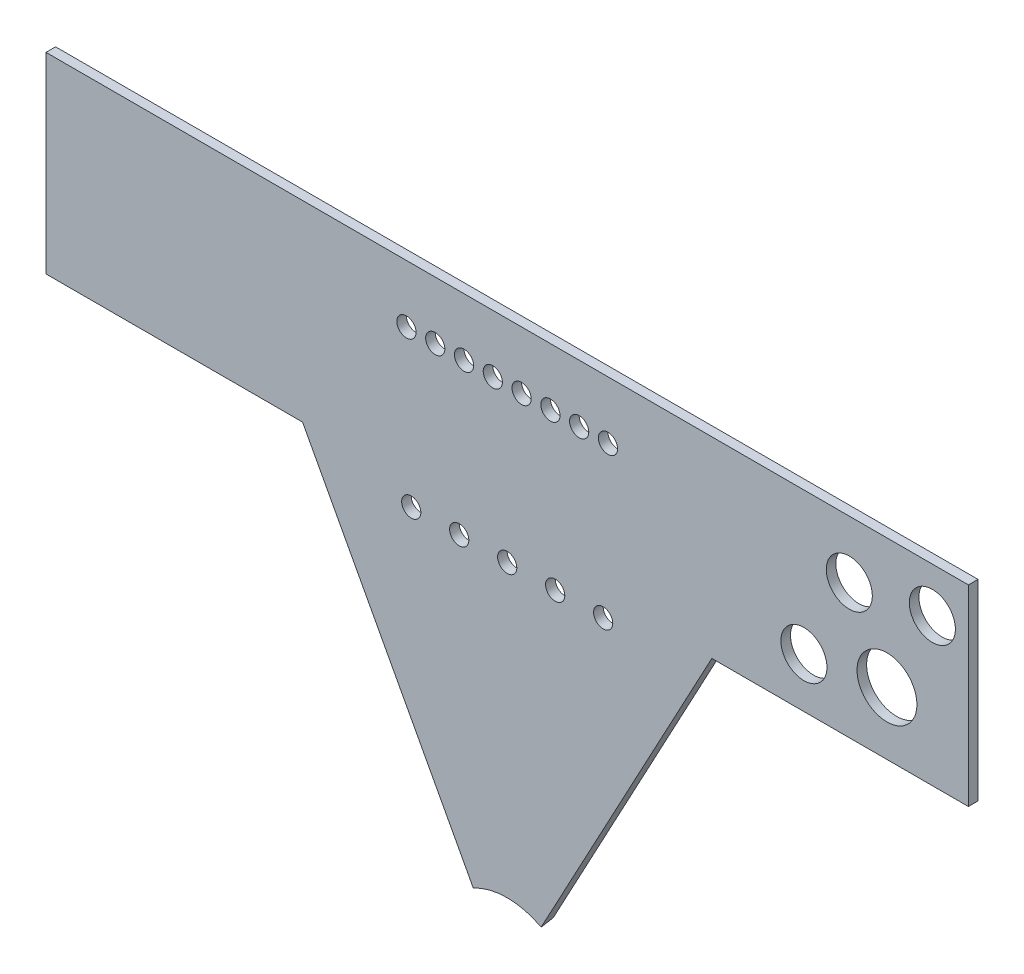
SolidWorks part; units mm, degrees
other "Markup1"
sketch "Sketch14" plane through (-149.406, -168.7453, 3.175) normal (0, 0, 1) x (1, 0, 0)
other "DetailItem1"
other "DetailItem2"
other "DetailItem3"
other "DetailItem4"
other "DetailItem5"
other "DetailItem6"
other "Markup2"
sketch "Sketch15" plane through (-149.406, -168.7453, 3.175) normal (0, 0, 1) x (1, 0, 0)
ref_plane "Front Plane" through (0, 0, 0) normal (0, 0, 1) x (1, 0, 0)
ref_plane "Top Plane" through (0, 0, 0) normal (0, 1, 0) x (1, 0, 0)
ref_plane "Right Plane" through (0, 0, 0) normal (1, 0, 0) x (0, 0, -1)
sketch "Sketch1" plane through (0, 0, 0) normal (0, 0, 1) x (1, 0, 0)
  line L0 (-101.781, 0) -> (101.781, 0)
  line L1 (-101.781, 0) -> (-12.0294, -167.2577)
  line L2 (101.781, 0) -> (12.0294, -167.2577)
  line L3 (0, -164.2341) -> (0, 0) construction
  arc A0 (-12.0294, -167.2577) -> (12.0294, -167.2577) centre (0, -189.6754) cw
  point P4 (0, 0)
  dimension "D1" = 203.5619
  dimension "D2" = 61.782
  dimension "D3" = 189.817
  dimension "D4" = 61.782
  dimension "D5" = 189.817
extrude "Boss-Extrude1" add sketch "Sketch1" along normal blind 3.175 draft 28
sketch "Sketch6" plane through (0, 0, 3.175) normal (0, 0, 1) x (1, 0, 0)
  line L0 (-101.781, 0) -> (101.781, 0)
  line L1 (101.781, 0) -> (103.6968, 0)
  line L2 (12.6904, -169.5964) -> (104.6027, 1.6882) construction
  line L3 (103.6968, 0) -> (104.6027, 1.6882)
  line L4 (104.6027, 1.6882) -> (-104.6027, 1.6882)
  line L5 (104.6027, 1.6882) -> (-104.6027, 1.6882) construction
  line L6 (-104.6027, 1.6882) -> (-103.6968, 0)
  line L7 (-103.6968, 0) -> (-101.781, 0)
  line L8 (-104.6027, 1.6882) -> (-12.6904, -169.5964) construction
  line L9 (-101.781, 0) -> (-11.2312, -168.7453)
  line L10 (-101.781, 0) -> (-12.0294, -167.2577) construction
  line L11 (-12.6904, -169.5964) -> (-103.6968, 0)
  line L12 (101.781, 0) -> (11.2312, -168.7453)
  line L14 (12.6904, -169.5964) -> (103.6968, 0)
  arc A0 (12.6904, -169.5964) -> (-12.6904, -169.5964) centre (0, -189.6754) ccw construction
  arc A2 (-11.2312, -168.7453) -> (-12.6904, -169.5964) centre (0, -189.6754) ccw
  arc A3 (11.2312, -168.7453) -> (12.6904, -169.5964) centre (0, -189.6754) cw
  line M7 (12.6904, -169.5964) -> (104.6027, 1.6882)
  line M9 (-104.6027, 1.6882) -> (-12.6904, -169.5964)
extrude "Cut-Extrude3" cut sketch "Sketch6" against normal through all contours A2 L9 L7 M9 | L12 A3 L1 M7
sketch "Sketch8" plane through (0, 0, 3.175) normal (0, 0, 1) x (1, 0, 0)
  line L0 (-101.781, 0) -> (-152.581, 0)
  line L1 (-152.581, 0) -> (-152.581, -63.5)
  line L2 (-152.581, -63.5) -> (-67.7065, -63.5)
  line L3 (-101.781, 0) -> (-12.0294, -167.2577) construction
  line L4 (-67.7065, -63.5) -> (-101.781, 0)
  line L5 (0, -1.7463) -> (0, 1.7463) construction
  line L6 (152.581, -63.5) -> (67.7065, -63.5)
  line L7 (101.781, 0) -> (152.581, 0)
  line L8 (152.581, 0) -> (152.581, -63.5)
  line L9 (67.7065, -63.5) -> (101.781, 0)
  dimension "D1" = 50.8
  dimension "D2" = 63.5
sketch "Sketch7" plane through (0, 0, 3.175) normal (0, 0, 1) x (1, 0, 0)
  line L0 (-98.3735, -6.35) -> (98.3735, -6.35) construction
  line L1 (-101.781, 0) -> (-12.0294, -167.2577) construction
  line L2 (101.781, 0) -> (12.0294, -167.2577) construction
  line L3 (-101.781, 0) -> (101.781, 0) construction
  line L4 (-83.9606, -6.35) -> (0.7672, -164.2457) construction
  circle A0 centre (-44.4493, -6.35) radius 1.016
  circle A1 centre (-31.7495, -6.35) radius 1.016
  circle A2 centre (-19.0497, -6.35) radius 1.016
  circle A3 centre (-6.3499, -6.35) radius 1.016
  circle A4 centre (6.3499, -6.35) radius 1.016
  circle A5 centre (19.0497, -6.35) radius 1.016
  circle A6 centre (31.7495, -6.35) radius 1.016
  circle A7 centre (44.4493, -6.35) radius 1.016
  arc A8 (12.0294, -167.2577) -> (-12.0294, -167.2577) centre (0, -189.6754) ccw construction
  circle A9 centre (-71.9506, -28.7313) radius 1.016
  dimension "D2" = 2.032
  dimension "D7" = 2.032
  dimension "D1" = 6.35
  dimension "D3" = 53.9242
  dimension "D5" = 53.9242
  dimension "D6" = 12.7
  dimension "D8" = 25.4
  dimension "D4" = 8
extrude "Boss-Extrude2" add sketch "Sketch8" against normal up to surface (3.175 mm away) up to face at (0, -82.873, 0)
sketch "Sketch9" plane through (0, 0, 3.175) normal (0, 0, 1) x (1, 0, 0)
  line L0 (0, 0) -> (0, -165.9223) construction
  line L1 (0, -165.9223) -> (33.8523, -158.9562) construction
  line L2 (-152.581, -19.05) -> (152.581, -19.05) construction
  line L3 (-152.581, 0) -> (-152.581, -63.5) construction
  line L4 (152.581, -63.5) -> (152.581, 0) construction
  line L5 (-152.581, 0) -> (152.581, 0) construction
  line L6 (153.5303, 9.145) -> (97.7491, -94.8067) construction
  line L7 (101.781, 0) -> (12.0294, -167.2577) construction
  line L8 (120.5165, -5.3742) -> (72.2981, -95.2324) construction
  arc A0 (11.2312, -168.7453) -> (-11.2312, -168.7453) centre (0, -189.6754) ccw construction
  circle A1 centre (125.6397, -42.8308) radius 9.906
  circle A2 centre (140.6521, -14.8542) radius 7.62
  circle A3 centre (113.178, -19.05) radius 7.62
  circle A4 centre (98.1656, -47.0266) radius 7.62
  point P19 (140.6521, -14.8542)
  point P20 (136.6993, -15.5058)
  point P21 (-33.3375, -19.05)
  point P22 (-23.8125, -19.05)
  point P23 (-14.2875, -19.05)
  point P24 (-4.7625, -19.05)
  point P31 (98.1656, -47.0266)
  point P32 (113.178, -19.05)
  point P37 (137.8545, -13.353)
  point P38 (113.1885, -19.05)
  point P39 (0, 0)
  dimension "D8" = 15.24
  dimension "D10" = 15.24
  dimension "D11" = 15.24
  dimension "D1" = 19.05
  dimension "D2" = 41.275
  dimension "D4" = 9.525
  dimension "D5" = 9.525
  dimension "D6" = 9.525
  dimension "D7" = 33.3375
  dimension "D9" = 22.225
  dimension "D12" = 31.75
  dimension "D3" = 31.75
hole_wizard "1/4 (0.25) Diameter Hole1" positions "Sketch10" profile "Sketch12" hole size "1/4" standard "ANSI Inch" end condition through all
sketch "Sketch10" plane through (0, 0, 3.175) normal (0, 0, 1) x (1, 0, 0)
  point P0 (-33.3375, -19.05)
  point P3 (-23.8125, -19.05)
  point P6 (-14.2875, -19.05)
  point P9 (-4.7625, -19.05)
sketch "Sketch12" plane through (-33.3375, -19.05, 3.175) normal (1, 0, 0) x (0, -1, 0)
  line L0 (0, 0) -> (0, 3.175)
  line L1 (0, 3.175) -> (3.175, 3.175)
  line L2 (3.175, 3.175) -> (3.175, 0)
  line L5 (3.175, 0) -> (0, 0)
  line L11 (0, -6.35) -> (0, 107.95) construction
  dimension "Thru Hole Dia." = 6.35
  dimension "Thru Hole Depth" = 3.175
ref_plane "Plane1" through (0, 0, 0) normal (1, 0, 0) x (0, 0, -1)
mirror "Mirror1" about plane through (0, 0, 0) normal (1, 0, 0) of "1/4 (0.25) Diameter Hole1"
extrude "Cut-Extrude4" cut sketch "Sketch9" against normal through all
sketch "Sketch16" plane through (0, 0, 3.175) normal (0, 0, 1) x (1, 0, 0)
  line L0 (-99.008, -69.85) -> (119.1387, -69.85) construction
  line L1 (0, -48.9613) -> (0, -108.1795) construction
  line L2 (-152.581, -63.5) -> (-67.7065, -63.5) construction
  point P7 (-15.875, -69.85)
  point P8 (-31.75, -69.85)
  point P9 (0, -69.85)
  point P10 (15.875, -69.85)
  point P11 (31.75, -69.85)
  dimension "D1" = 6.35
  dimension "D2" = 15.875
  dimension "D3" = 15.875
  dimension "D4" = 15.875
  dimension "D5" = 15.875
hole_wizard "1/4 (0.25) Diameter Hole2" positions "Sketch17" profile "Sketch18" hole size "1/4" standard "ANSI Inch" end condition through all
sketch "Sketch17" plane through (0, 0, 3.175) normal (0, 0, 1) x (1, 0, 0)
  point P0 (-31.75, -69.85)
  point P3 (-15.875, -69.85)
  point P6 (0, -69.85)
  point P9 (15.875, -69.85)
  point P12 (31.75, -69.85)
sketch "Sketch18" plane through (-31.75, -69.85, 3.175) normal (1, 0, 0) x (0, -1, 0)
  line L0 (0, 0) -> (0, 3.175)
  line L1 (0, 3.175) -> (3.175, 3.175)
  line L2 (3.175, 3.175) -> (3.175, 0)
  line L5 (3.175, 0) -> (0, 0)
  line L11 (0, -6.35) -> (0, 107.95) construction
  dimension "Thru Hole Dia." = 6.35
  dimension "Thru Hole Depth" = 3.175
equation "\"D4@Sketch1\"=\"D2@Sketch1\""
equation "\"D5@Sketch1\"=\"D3@Sketch1\""
equation "\"D5@Sketch7\"=\"D3@Sketch7\""
equation "\"D7@Sketch9\"=3.5*\"D4@Sketch9\""
equation "\"D5@Sketch9\"=\"D4@Sketch9\""
equation "\"D6@Sketch9\"=\"D4@Sketch9\""
equation "\"D3@Sketch16\"=\"D2@Sketch16\""
equation "\"D4@Sketch16\"=\"D2@Sketch16\""
equation "\"D5@Sketch16\"=\"D2@Sketch16\""
